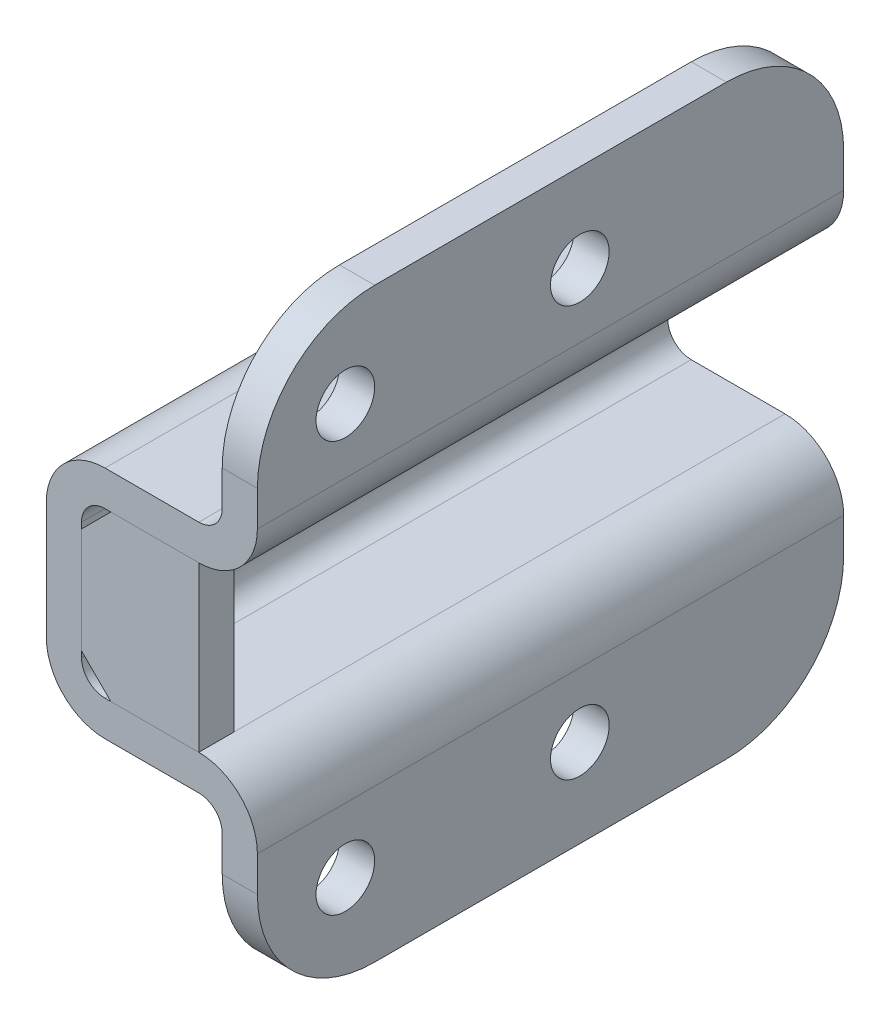
SolidWorks part; units mm, degrees
material "普通碳钢"
ref_plane "Front" through (0, 0, 0) normal (0, 0, 1) x (1, 0, 0)
ref_plane "Top" through (0, 0, 0) normal (0, 1, 0) x (1, 0, 0)
ref_plane "Right" through (0, 0, 0) normal (1, 0, 0) x (0, 0, -1)
sketch "草图1" plane through (0, 0, 0) normal (0, 0, 1) x (1, 0, 0)
  line L0 (0, 10) -> (0, 30)
  line L5 (10, 40) -> (26, 40)
  line L6 (30, 44) -> (30, 70)
  line L14 (30, -30) -> (30, -4)
  line L15 (26, 0) -> (10, 0)
  line L16 (36, -30) -> (36, -4)
  line L17 (26, 6) -> (10, 6)
  line L18 (6, 10) -> (6, 30)
  line L19 (10, 34) -> (26, 34)
  line L20 (36, 44) -> (36, 70)
  line L21 (30, 70) -> (36, 70)
  line L22 (30, -30) -> (36, -30)
  arc A0 (0, 10) -> (10, 0) centre (10, 10) ccw
  arc A1 (0, 30) -> (10, 40) centre (10, 30) cw
  arc A2 (30, -4) -> (26, 0) centre (26, -4) ccw
  arc A3 (26, 40) -> (30, 44) centre (26, 44) ccw
  arc A4 (36, -4) -> (26, 6) centre (26, -4) ccw
  arc A5 (6, 10) -> (10, 6) centre (10, 10) ccw
  arc A6 (6, 30) -> (10, 34) centre (10, 30) cw
  arc A7 (26, 34) -> (36, 44) centre (26, 44) ccw
  point P8 (0, 0)
  point P11 (0, 40)
  point P16 (30, 0)
  point P19 (30, 40)
  dimension "D6" = 10
  dimension "D7" = 4
  dimension "D1" = 40
  dimension "D2" = 30
  dimension "D3" = 30
  dimension "D4" = 30
  dimension "D5" = 30
  dimension "D8" = 6
extrude "凸台-拉伸1" add sketch "草图1" along normal blind 100
sketch "草图2" plane through (0, 0, 0) normal (-1, 0, 0) x (0, 0, 1)
  line L0 (0, 30) -> (0, 10) construction
  line L3 (100, 30) -> (0, 30) construction
  circle A0 centre (20, 20) radius 5
  dimension "D1" = 10
  dimension "D2" = 20
  dimension "D3" = 10
extrude "切除-拉伸1" cut sketch "草图2" against normal up to next
sketch "草图3" plane through (30, 0, 0) normal (-1, 0, 0) x (0, 0, 1)
  line L0 (65, 70) -> (65, -30) construction
  line L1 (100, 70) -> (0, 70) construction
  line L2 (100, -30) -> (0, -30) construction
  line L3 (45, 70) -> (45, -30) construction
  line L4 (85, 70) -> (85, -30) construction
  line L5 (100, 70) -> (100, 44) construction
  line L9 (45, -15) -> (85, -15) construction
  line L12 (45, 55) -> (85, 55) construction
  circle A12 centre (85, 55) radius 5
  circle A13 centre (45, 55) radius 5
  circle A14 centre (45, -15) radius 5
  circle A15 centre (85, -15) radius 5
  dimension "D7" = 15
  dimension "D3" = 10
  dimension "D1" = 20
  dimension "D9" = 15
  dimension "D4" = 35
  dimension "D2" = 20
extrude "切除-拉伸2" cut sketch "草图3" against normal up to next
sketch "草图4" plane through (0, 0, 100) normal (0, 0, 1) x (1, 0, 0)
  line L0 (10, 34) -> (26, 34) construction
  line L1 (11, 34) -> (26, 34)
  line L2 (6, 10) -> (6, 30) construction
  line L3 (6, 11) -> (6, 29)
  line L4 (26, 6) -> (10, 6) construction
  line L5 (26, 6) -> (11, 6)
  line L6 (26, 34) -> (26, 6)
  line L7 (6, 29) -> (11, 34)
  line L8 (11, 6) -> (6, 11)
  point P8 (6, 34)
  point P11 (6, 6)
extrude "凸台-拉伸2" add sketch "草图4" against normal blind 6 separate body
fillet "圆角1" radius 20 4 edges at (33, -30, 100) (33, 70, 100) (33, 70, 0) (33, -30, 0)
